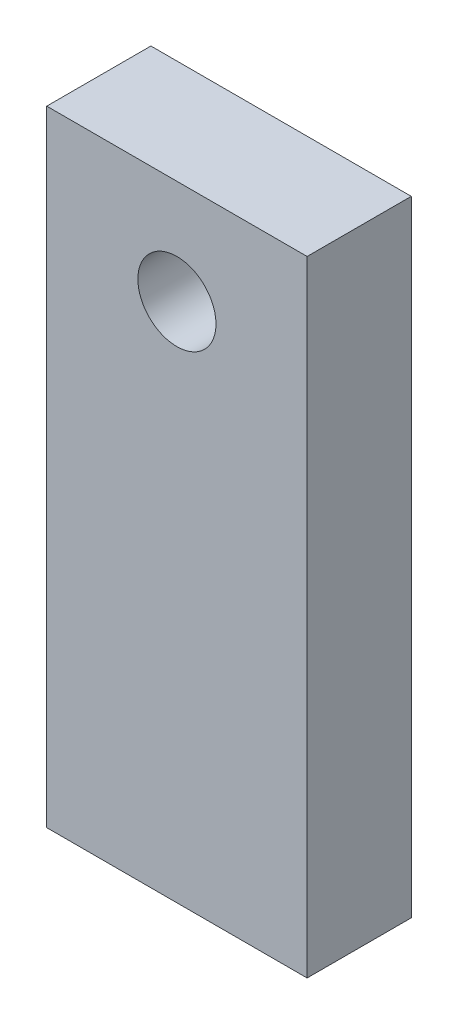
SolidWorks part; units mm, degrees
ref_plane "Ebene vorne" through (0, 0, 0) normal (0, 0, 1) x (1, 0, 0)
ref_plane "Ebene oben" through (0, 0, 0) normal (0, 1, 0) x (1, 0, 0)
ref_plane "Ebene rechts" through (0, 0, 0) normal (1, 0, 0) x (0, 0, -1)
sketch "Holes" plane through (0, 0, 0) normal (0, 0, 1) x (1, 0, 0)
  circle A0 centre (0, 610) radius 3
  circle A1 centre (90, 610) radius 3
sketch "Thickness" plane through (0, 0, 0) normal (1, 0, 0) x (0, 0, -1)
  line L0 (4, 610) -> (-4, 610)
  point P7 (0, 610)
sketch "Baseplate" plane through (0, 0, 0) normal (0, 0, 1) x (1, 0, 0)
  line L1 (-12.6, 570) -> (23.35, 570)
  line L2 (-12.6, 570) -> (-12.6, 564)
  line L3 (-12.6, 564) -> (23.35, 564)
  line L4 (23.35, 570) -> (23.35, 564)
  circle A0 centre (19.35, 566.9539) radius 1.25
  circle A1 centre (-8, 566.9539) radius 1.25
sketch "Skizze4" plane through (0, 0, 0) normal (0, 0, 1) x (1, 0, 0)
  line L0 (-10, 610) -> (-10, 570)
  line L1 (-10, 570) -> (10, 570)
  line L2 (10, 570) -> (10, 610)
  line L3 (-10, 610) -> (-10, 618)
  line L4 (-10, 618) -> (10, 618)
  line L5 (10, 618) -> (10, 610)
  circle A1 centre (0, 610) radius 3
  dimension "D1" = 20
  dimension "D2" = 8
extrude "Aufsatz-Linear austragen1" add sketch "Skizze4" along normal up to vertex (4 mm away) and the other way up to vertex (4 mm away) contours L2 L5 L4 L3 L0 L1 | A1 up to point (0, 610, 4) other way up to point (0, 610, -4)
